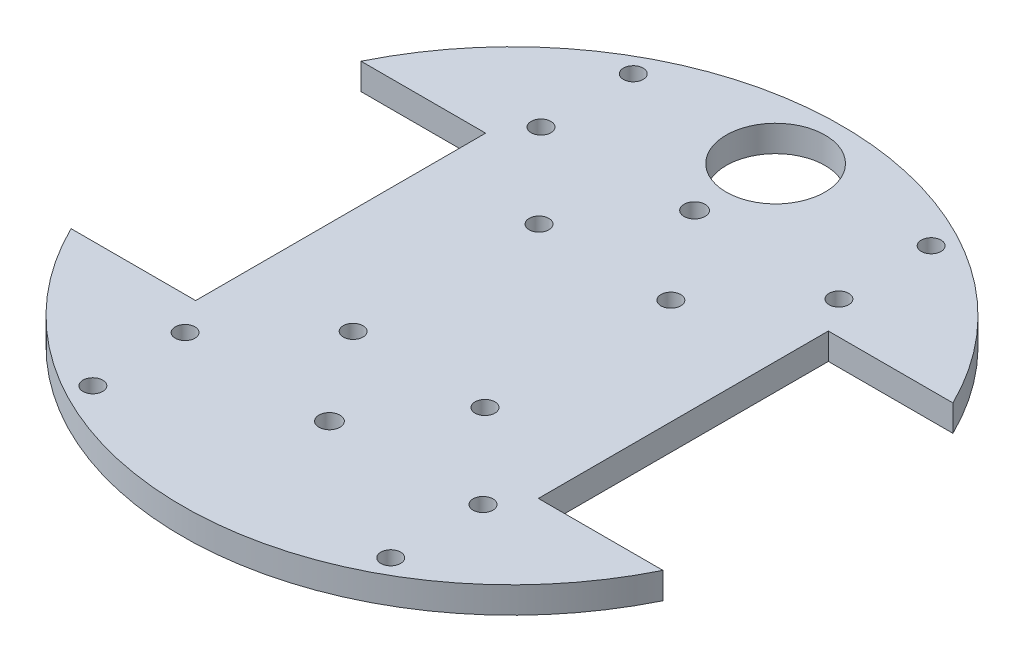
SolidWorks part; units mm, degrees
ref_plane "Front Plane" through (0, 0, 0) normal (0, 0, 1) x (1, 0, 0)
ref_plane "Top Plane" through (0, 0, 0) normal (0, 1, 0) x (1, 0, 0)
ref_plane "Right Plane" through (0, 0, 0) normal (1, 0, 0) x (0, 0, -1)
sketch "Sketch1" plane through (0, 0, 0) normal (0, 1, 0) x (1, 0, 0)
  line L0 (0, 50) -> (0, -50) construction
  line L1 (-50, 0) -> (50, 0) construction
  line L2 (-50, 20.7263) -> (-50, -21.0382) construction
  line L5 (-26, 22) -> (-44.8999, 22)
  line L6 (26, 42.7083) -> (26, -42.7083)
  line L7 (-26, 42.7083) -> (-26, -42.7083)
  line L8 (-26, -22) -> (-44.8999, -22)
  line L9 (26, -22) -> (44.8999, -22)
  line L10 (26, 22) -> (44.8999, 22)
  line L11 (0, -16.6134) -> (0, -14.6134)
  line L18 (-20, -20.1134) -> (20, -20.1134) construction
  circle A0 centre (0, 0) radius 50
  circle A1 centre (0, 40) radius 7.5
  circle A7 centre (-10, 14.1) radius 1.5
  circle A9 centre (-10, -14.1) radius 1.5
  circle A10 centre (10, 14.1) radius 1.5
  circle A11 centre (10, -14.1) radius 1.5
  circle A16 centre (0, -27.7) radius 1.6 construction
  circle A17 centre (0, 27.7) radius 1.6 construction
  circle A18 centre (0, -27.7) radius 1.6
  circle A19 centre (0, 27.7) radius 1.6
  circle A22 centre (22.6, -41) radius 1.5
  circle A26 centre (-22.6, 41) radius 1.5
  circle A27 centre (-22.6, 27) radius 1.5
  circle A28 centre (22.6, 41) radius 1.5
  circle A29 centre (22.6, 27) radius 1.5
  circle A36 centre (-22.6, -41) radius 1.5
  circle A37 centre (-22.6, -27) radius 1.5
  circle A38 centre (22.6, -27) radius 1.5
  point P44 (20, -23.6134)
  point P47 (20, -16.6134)
  point P80 (6, -14.6134)
  point P83 (-6, -14.6134)
  dimension "D1" = 100
  dimension "D2" = 3
  dimension "D3" = 14.1
  dimension "D4" = 40
  dimension "D11" = 3.4
  dimension "D22" = 3
  dimension "D8" = 5
  dimension "D19" = 19
  dimension "D21" = 3
  dimension "D23" = 5
  dimension "D24" = 19
  dimension "D25" = 3.4
  dimension "D26" = 3.4
  dimension "D27" = 3
  dimension "D28" = 3
  dimension "D6" = 15
  dimension "D5" = 26
  dimension "D7" = 22
  dimension "D9" = 3.4
  dimension "D10" = 7
  dimension "D20" = 6
extrude "Boss-Extrude1" add sketch "Sketch1" along normal blind 4
